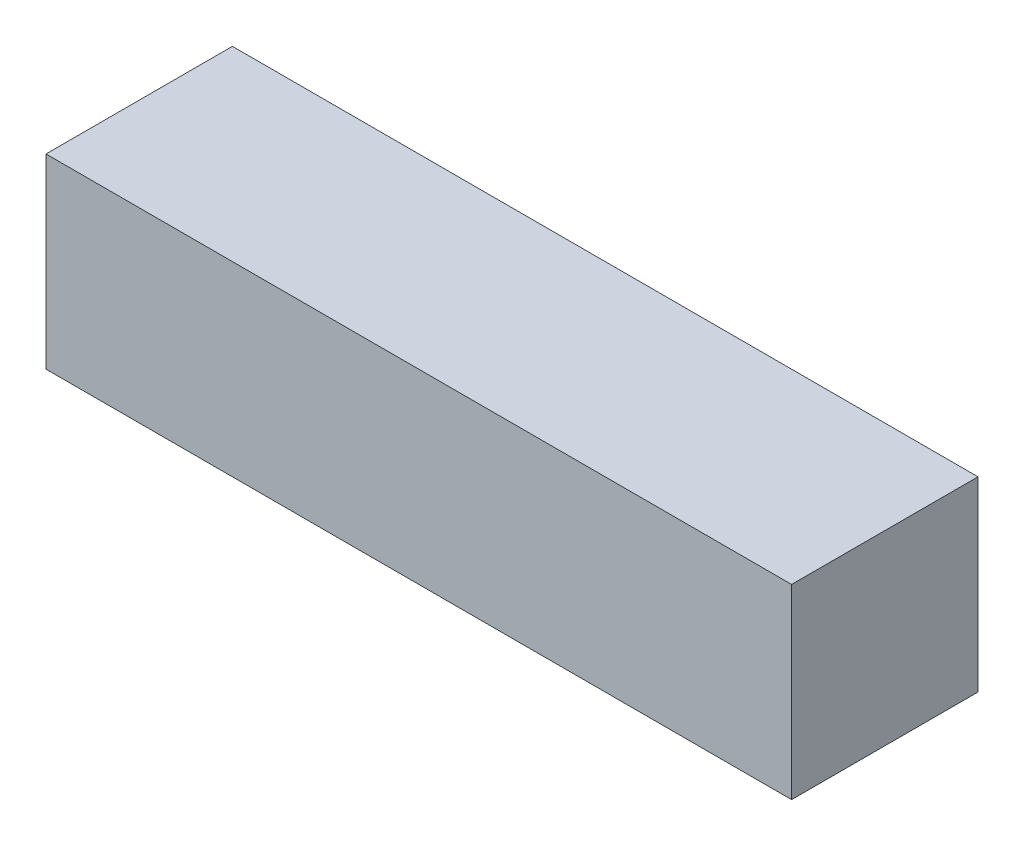
SolidWorks part; units mm, degrees
material "Plywood"
ref_plane "Front Plane" through (0, 0, 0) normal (0, 0, 1) x (1, 0, 0)
ref_plane "Top Plane" through (0, 0, 0) normal (0, 1, 0) x (1, 0, 0)
ref_plane "Right Plane" through (0, 0, 0) normal (1, 0, 0) x (0, 0, -1)
sketch "Sketch1" plane through (0, 0, 0) normal (1, 0, 0) x (0, 0, -1)
  line L1 (-4.7625, 4.7625) -> (4.7625, 4.7625)
  line L2 (-4.7625, 4.7625) -> (-4.7625, -4.7625)
  line L3 (-4.7625, -4.7625) -> (4.7625, -4.7625)
  line L4 (4.7625, 4.7625) -> (4.7625, -4.7625)
  point P4 (-4.7625, 0)
  point P5 (0, 4.7625)
  dimension "D1" = 9.525
extrude "Boss-Extrude1" add sketch "Sketch1" along normal mid plane 38.1
move or copy body "Body-Move/Copy1" [suppressed] bodies to move or copy 101 parameters "D1"=0, "D2"=0, "D3"=0
